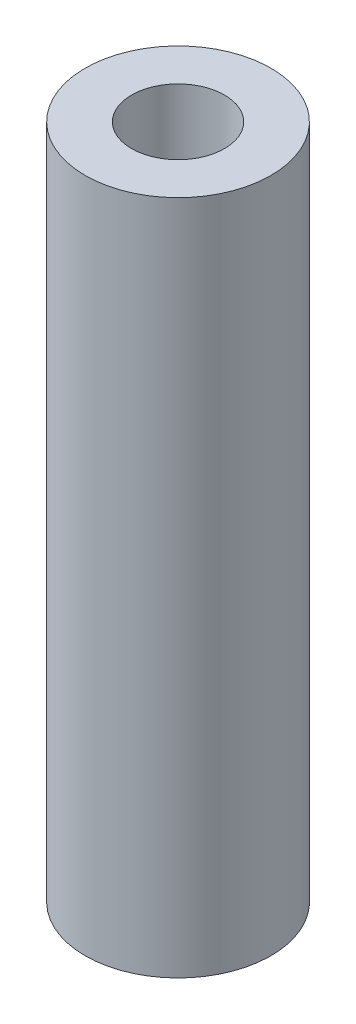
SolidWorks part; units mm, degrees
ref_plane "Front Plane" through (0, 0, 0) normal (0, 0, 1) x (1, 0, 0)
ref_plane "Top Plane" through (0, 0, 0) normal (0, 1, 0) x (1, 0, 0)
ref_plane "Right Plane" through (0, 0, 0) normal (1, 0, 0) x (0, 0, -1)
sketch "Sketch1" plane through (0, 0, 0) normal (0, 1, 0) x (1, 0, 0)
  circle A0 centre (0, 0) radius 5.5
  circle A1 centre (0, 0) radius 11
  dimension "D1" = 11
  dimension "D2" = 22
extrude "Boss-Extrude1" add sketch "Sketch1" along normal blind 80
